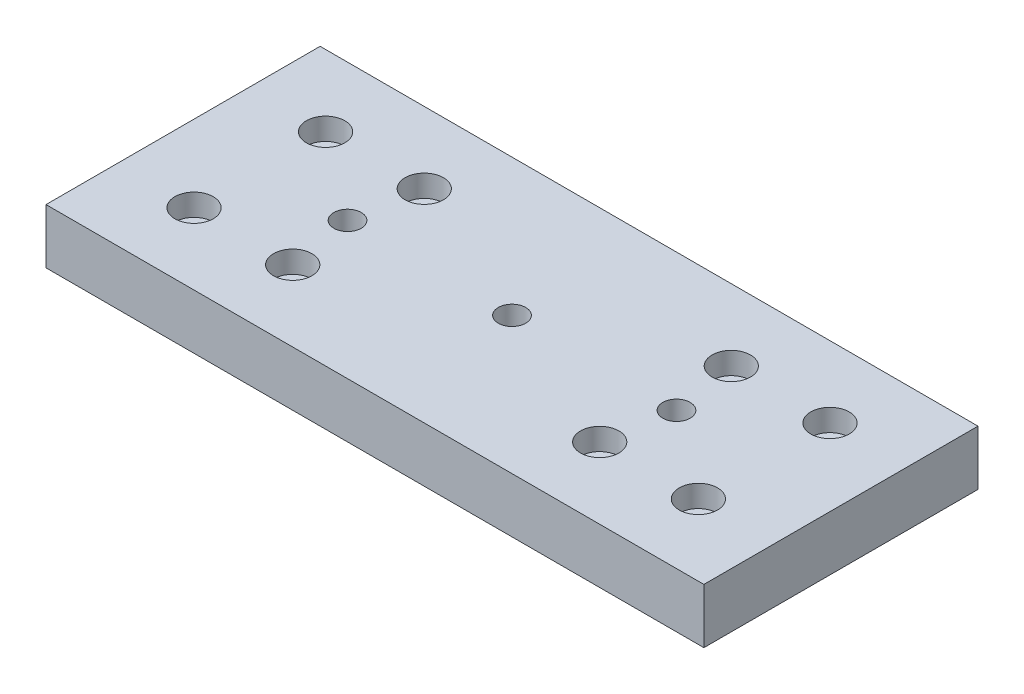
SolidWorks part; units mm, degrees
ref_plane "Front Plane" through (0, 0, 0) normal (0, 0, 1) x (1, 0, 0)
ref_plane "Top Plane" through (0, 0, 0) normal (0, 1, 0) x (1, 0, 0)
ref_plane "Right Plane" through (0, 0, 0) normal (1, 0, 0) x (0, 0, -1)
sketch "Sketch1" plane through (0, 0, 0) normal (0, 1, 0) x (1, 0, 0)
  line L1 (60, -25) -> (-60, -25)
  line L2 (60, -25) -> (60, 25)
  line L3 (60, 25) -> (-60, 25)
  line L4 (-60, -25) -> (-60, 25)
  line L5 (60, -25) -> (-60, 25) construction
  line L6 (60, 25) -> (-60, -25) construction
  point P0 (0, 0)
  dimension "D1" = 50
  dimension "D2" = 120
extrude "Boss-Extrude1" add sketch "Sketch1" along normal blind 10
sketch "Sketch2" plane through (0, 10, 0) normal (0, 1, 0) x (1, 0, 0)
  line L0 (-60, 0) -> (0, 0) construction
  line L1 (-60, 25) -> (-60, -25) construction
  line L2 (0, 0) -> (0, 25) construction
  line L3 (60, 25) -> (-60, 25) construction
  circle A0 centre (-28, -12) radius 1.5
  circle A1 centre (-46, -12) radius 1.5
  circle A3 centre (28, -12) radius 1.5
  circle A5 centre (46, -12) radius 1.5
  circle A7 centre (46, 12) radius 1.5
  circle A9 centre (28, 12) radius 1.5
  circle A12 centre (-46, 12) radius 1.5
  circle A16 centre (-28, 12) radius 1.5
  dimension "D1" = 3
  dimension "D2" = 24
  dimension "D3" = 18
  dimension "D4" = 14
extrude "Linear_bearing_mount" cut sketch "Sketch2" against normal through all
sketch "Sketch3" plane through (0, 0, 0) normal (0, -1, 0) x (1, 0, 0)
  line L2 (60, 25) -> (60, -25) construction
  circle A0 centre (0, 0) radius 2.5
  circle A1 centre (30, 0) radius 2.5
  circle A2 centre (-30, 0) radius 2.5
  dimension "D1" = 5
  dimension "D2" = 30
  dimension "D3" = 30
  dimension "D5" = 30
extrude "Surface_profile_mount" cut sketch "Sketch3" against normal through all
sketch "Sketch4" plane through (0, 0, 0) normal (0, -1, 0) x (1, 0, 0)
  circle A0 centre (30, 0) radius 4.25
  circle A1 centre (0, 0) radius 4.25
  circle A2 centre (-30, 0) radius 4.25
  dimension "D1" = 8.5
extrude "Surf.prof.mount_countersink" cut sketch "Sketch4" against normal blind 5
sketch "Sketch5" plane through (0, 10, 0) normal (0, 1, 0) x (1, 0, 0)
  line L0 (0, 25) -> (0, 0) construction
  line L1 (60, 25) -> (-60, 25) construction
  line L2 (0, 0) -> (-60, 0) construction
  line L3 (-60, 25) -> (-60, -25) construction
  circle A0 centre (-46, 12) radius 3.5
  circle A1 centre (-28, 12) radius 3.5
  circle A2 centre (-28, -12) radius 3.5
  circle A3 centre (-46, -12) radius 3.5
  circle A4 centre (46, -12) radius 3.5
  circle A5 centre (28, -12) radius 3.5
  circle A6 centre (28, 12) radius 3.5
  circle A7 centre (46, 12) radius 3.5
  dimension "D1" = 7
extrude "Cut-Extrude1" cut sketch "Sketch5" against normal blind 4
